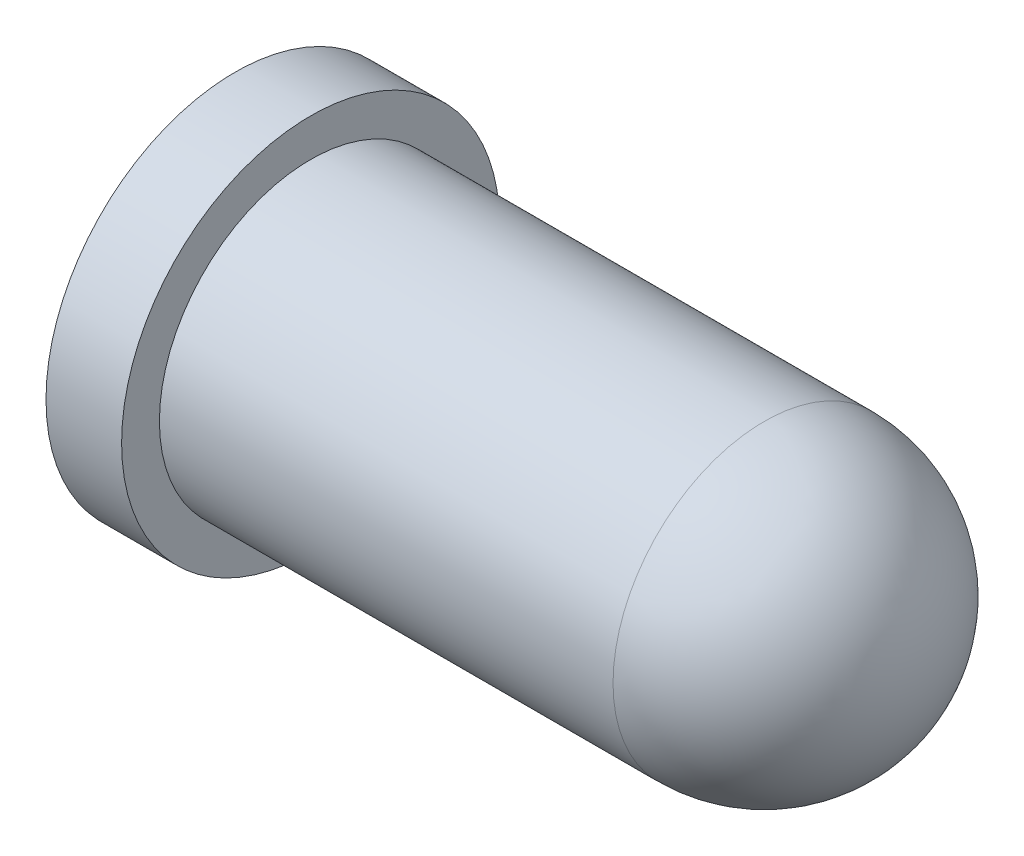
SolidWorks part; units mm, degrees
ref_plane "Front Plane" through (0, 0, 0) normal (0, 0, 1) x (1, 0, 0)
ref_plane "Top Plane" through (0, 0, 0) normal (0, 1, 0) x (1, 0, 0)
ref_plane "Right Plane" through (0, 0, 0) normal (1, 0, 0) x (0, 0, -1)
sketch "Sketch1" plane through (0, 0, 0) normal (1, 0, 0) x (0, 0, -1)
  circle A0 centre (0, 0) radius 2.5
extrude "Boss-Extrude1" add sketch "Sketch1" along normal blind 1
sketch "Sketch2" plane through (1, 0, 0) normal (1, 0, 0) x (0, 0, -1)
  circle A0 centre (0, 0) radius 2
extrude "Boss-Extrude2" add sketch "Sketch2" along normal blind 8
fillet "Fillet2" radius 2 1 edges at (9, 0, -2)
